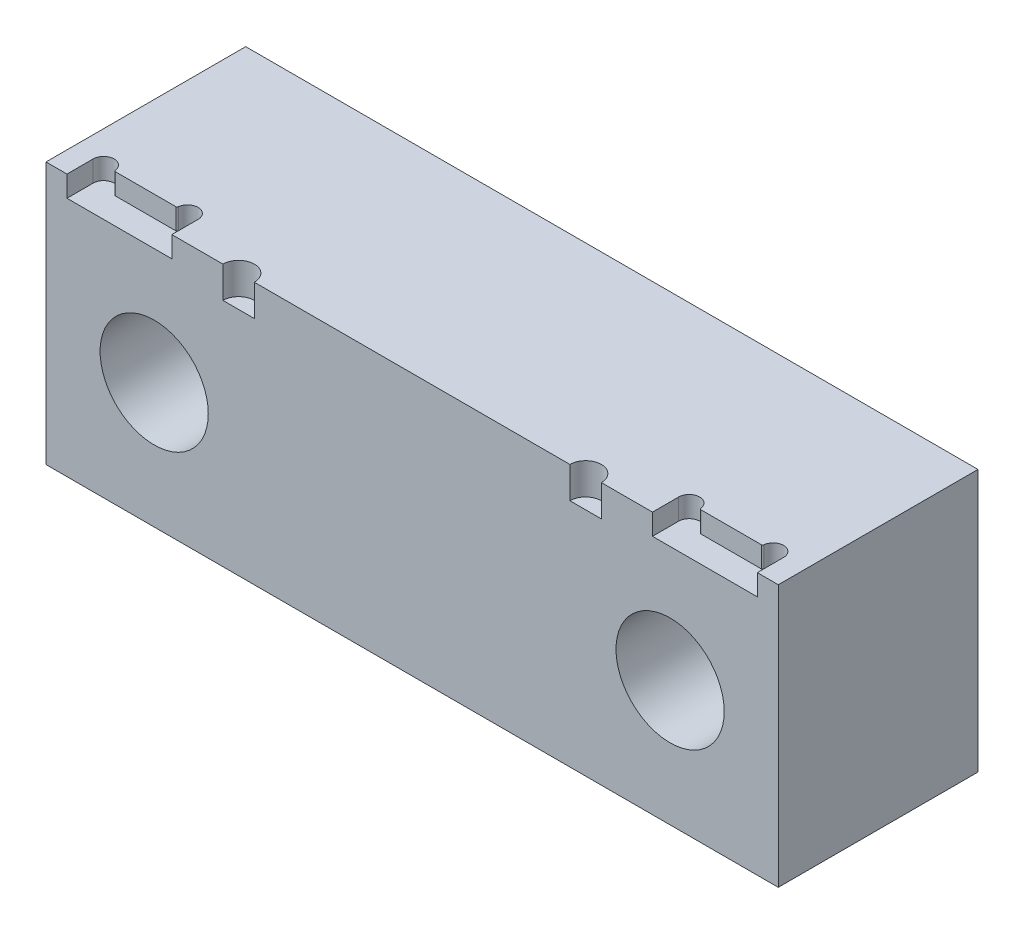
SolidWorks part; units mm, degrees
ref_plane "Front Plane" through (0, 0, 0) normal (0, 0, 1) x (1, 0, 0)
ref_plane "Top Plane" through (0, 0, 0) normal (0, 1, 0) x (1, 0, 0)
ref_plane "Right Plane" through (0, 0, 0) normal (1, 0, 0) x (0, 0, -1)
sketch "Sketch1" plane through (0, 0, 0) normal (1, 0, 0) x (0, 0, -1)
  line L1 (-19.05, -25) -> (19.05, -25)
  line L2 (-19.05, -25) -> (-19.05, 25)
  line L3 (-19.05, 25) -> (19.05, 25)
  line L4 (19.05, -25) -> (19.05, 25)
  line L5 (-19.05, -25) -> (19.05, 25) construction
  line L6 (-19.05, 25) -> (19.05, -25) construction
  point P0 (0, 0)
  dimension "D1" = 38.1
  dimension "D2" = 50
extrude "Boss-Extrude1" add sketch "Sketch1" along normal mid plane 139.7
hole_wizard "CBORE for 1/2 Socket Head Cap Screw1" positions "Sketch2" profile "Sketch3" counterbore size "1/2" standard "ANSI Inch" end condition through all
sketch "Sketch2" plane through (0, 0, 19.05) normal (0, 0, 1) x (1, 0, 0)
  line L0 (69.85, -25) -> (-69.85, -25) construction
  point P0 (-49.2125, -1.124)
  point P2 (49.2125, -1.124)
  dimension "D1" = 23.876
  dimension "D2" = 98.425
  dimension "D3" = 49.2125
sketch "Sketch3" plane through (-49.2125, -1.124, 19.05) normal (1, 0, 0) x (0, -1, 0)
  line L0 (0, 0) -> (0, 38.1)
  line L1 (0, 38.1) -> (6.9456, 38.1)
  line L3 (6.9456, 38.1) -> (6.9456, 27.94)
  line L4 (6.9456, 27.94) -> (10.3187, 27.94)
  line L5 (10.3187, 27.94) -> (10.3187, 0)
  line L7 (10.3187, 0) -> (0, 0)
  line L11 (0, -6.35) -> (0, 107.95) construction
  dimension "Thru Hole Dia." = 13.8913
  dimension "Thru Hole Depth" = 38.1
  dimension "C'Bore Dia." = 20.6375
  dimension "C'Bore Depth" = 27.94
sketch "Sketch4" plane through (0, -25, 0) normal (0, -1, 0) x (-1, 0, 0)
  text T0 "BOTTOM"
sketch "Sketch5" plane through (0, 25, 0) normal (0, 1, 0) x (1, 0, 0)
  line L0 (69.85, -19.05) -> (-69.85, -19.05) construction
  line L1 (-69.85, 19.05) -> (-69.85, -19.05) construction
  line L2 (-36.1, -19.05) -> (-30.1, -19.05)
  line L3 (0, 0) -> (0, -19.05) construction
  line L4 (36.1, -19.05) -> (30.1, -19.05)
  arc A0 (-36.1, -19.05) -> (-30.1, -19.05) centre (-33.1, -19.05) cw
  arc A1 (36.1, -19.05) -> (30.1, -19.05) centre (33.1, -19.05) ccw
  dimension "D1" = 36.75
  dimension "D2" = 3
extrude "Cut-Extrude1" cut sketch "Sketch5" against normal blind 6
sketch "Sketch7" plane through (0, 25, 0) normal (0, 1, 0) x (1, 0, 0)
  line L0 (-65.85, -19.05) -> (-65.85, -14.05)
  line L1 (-36.1, -19.05) -> (-69.85, -19.05) construction
  line L2 (-61.85, -14.05) -> (-49.85, -14.05)
  line L3 (-45.85, -19.05) -> (-45.85, -14.05)
  line L4 (-65.85, -19.05) -> (-45.85, -19.05)
  line L5 (-69.85, 19.05) -> (-69.85, -19.05) construction
  line L6 (0, 0) -> (0, -19.05) construction
  line L7 (30.1, -19.05) -> (-30.1, -19.05) construction
  line L8 (45.85, -19.05) -> (45.85, -14.05)
  line L9 (61.85, -14.05) -> (49.85, -14.05)
  line L10 (65.85, -19.05) -> (45.85, -19.05)
  line L11 (65.85, -19.05) -> (65.85, -14.05)
  arc A0 (-65.85, -14.05) -> (-61.85, -14.05) centre (-63.85, -14.05) cw
  arc A1 (-45.85, -14.05) -> (-49.85, -14.05) centre (-47.85, -14.05) ccw
  arc A2 (45.85, -14.05) -> (49.85, -14.05) centre (47.85, -14.05) cw
  arc A3 (65.85, -14.05) -> (61.85, -14.05) centre (63.85, -14.05) ccw
  line M7 (36.1, -19.05) -> (69.85, -19.05)
  dimension "D3" = 2
  dimension "D4" = 2
  dimension "D1" = 20
  dimension "D2" = 4
  dimension "D5" = 5
extrude "Cut-Extrude2" cut sketch "Sketch7" against normal blind 4 contours L11 A3 L9 A2 L8 M7 | L2 A1 L3 L4 L0 A0
sketch "Sketch8" plane through (0, 25, 0) normal (0, 1, 0) x (1, 0, 0)
  line L1 (-69.85, -19.05) -> (69.85, -19.05)
  line L2 (-69.85, -19.05) -> (-69.85, 19.05)
  line L3 (-69.85, 19.05) -> (69.85, 19.05)
  line L4 (69.85, -19.05) -> (69.85, 19.05)
fillet "Fillet1" radius 0.254 4 edges at (-61.85, 23, 14.05) (-49.85, 23, 14.05) (49.85, 23, 14.05) (61.85, 23, 14.05)
